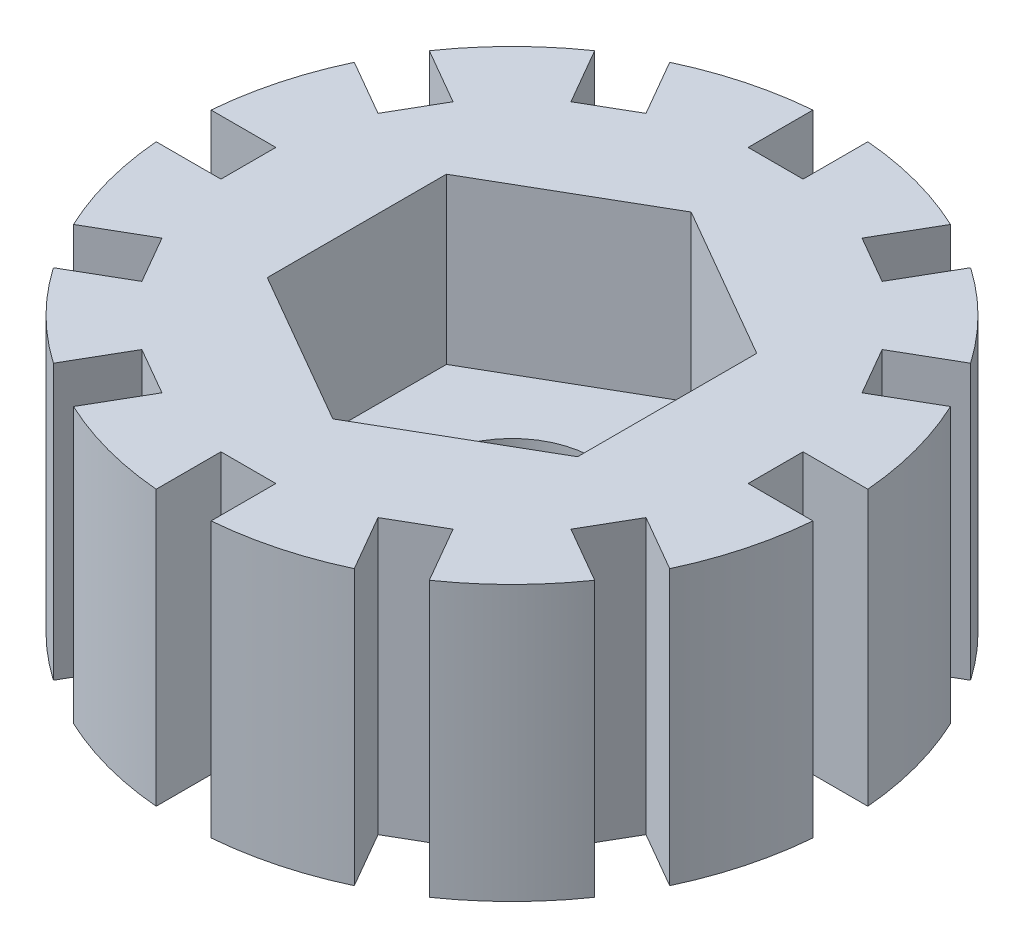
SolidWorks part; units mm, degrees
ref_plane "Front Plane" through (0, 0, 0) normal (0, 0, 1) x (1, 0, 0)
ref_plane "Top Plane" through (0, 0, 0) normal (0, 1, 0) x (1, 0, 0)
ref_plane "Right Plane" through (0, 0, 0) normal (1, 0, 0) x (0, 0, -1)
sketch "Sketch1" plane through (0, 0, 0) normal (0, 1, 0) x (1, 0, 0)
  circle A0 centre (0, 0) radius 1.5
  circle A1 centre (0, 0) radius 6
  dimension "D1" = 12
  dimension "D2" = 3
extrude "Boss-Extrude1" add sketch "Sketch1" along normal blind 5
sketch "Sketch6" plane through (0, 5, 0) normal (0, 1, 0) x (1, 0, 0)
  line L1 (2.825, -1.631) -> (2.825, 1.631)
  line L2 (2.825, 1.631) -> (0, 3.262)
  line L3 (0, 3.262) -> (-2.825, 1.631)
  line L4 (-2.825, 1.631) -> (-2.825, -1.631)
  line L5 (-2.825, -1.631) -> (0, -3.262)
  line L6 (0, -3.262) -> (2.825, -1.631)
  circle A0 centre (0, 0) radius 2.825 construction
  dimension "D1" = 5.65
extrude "Cut-Extrude1" cut sketch "Sketch6" against normal blind 3
sketch "Sketch7" plane through (0, 5, 0) normal (0, 1, 0) x (1, 0, 0)
  line L0 (0, 0) -> (0, 9.6911) construction
  line L2 (-0.5, 11.9468) -> (0.5, 11.9468)
  line L3 (-0.5, 11.9468) -> (-0.5, 4.8)
  line L4 (-0.5, 4.8) -> (0.5, 4.8)
  line L5 (0.5, 11.9468) -> (0.5, 4.8)
  line L6 (-0.5, 11.9468) -> (0.5, 4.8) construction
  line L7 (-0.5, 4.8) -> (0.5, 11.9468) construction
  circle A0 centre (0, 0) radius 6 construction
  point P3 (0, 8.3734)
  dimension "D1" = 1
  dimension "D2" = 1.2
extrude "Cut-Extrude2" cut sketch "Sketch7" against normal blind 10
pattern_circular "CirPattern1" count 12 over 360 about axis through (0, 0, 0) along (0, 1, 0) of "Cut-Extrude2"
